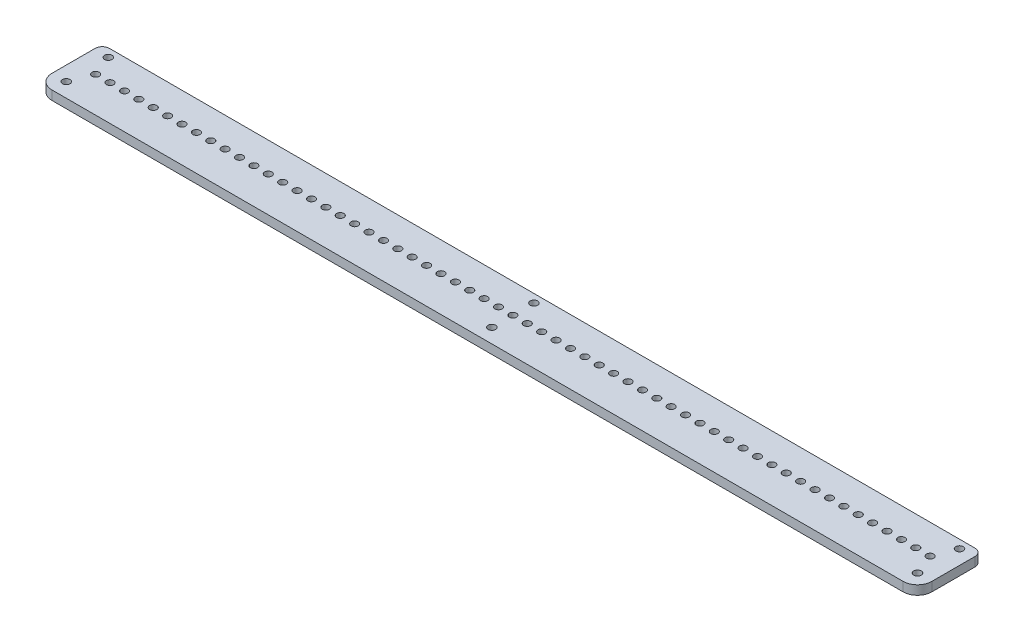
SolidWorks part; units mm, degrees
ref_plane "Front Plane" through (0, 0, 0) normal (0, 0, 1) x (1, 0, 0)
ref_plane "Top Plane" through (0, 0, 0) normal (0, 1, 0) x (1, 0, 0)
ref_plane "Right Plane" through (0, 0, 0) normal (1, 0, 0) x (0, 0, -1)
sketch "Sketch1" plane through (0, 0, 0) normal (0, 1, 0) x (1, 0, 0)
  line L1 (10, 0) -> (601.6, 0)
  line L2 (0, 10) -> (0, 40)
  line L3 (5, 45) -> (606.6, 45)
  line L4 (611.6, 10) -> (611.6, 40)
  line L5 (0, 0) -> (611.6, 45) construction
  line L6 (0, 45) -> (611.6, 0) construction
  arc A0 (0, 10) -> (10, 0) centre (10, 10) ccw
  arc A1 (611.6, 10) -> (601.6, 0) centre (601.6, 10) cw
  arc A2 (0, 40) -> (5, 45) centre (5, 40) cw
  arc A3 (611.6, 40) -> (606.6, 45) centre (606.6, 40) ccw
  point P4 (305.8, 22.5)
  dimension "D3" = 10
  dimension "D4" = 5
  dimension "D1" = 45
  dimension "D2" = 611.6
extrude "Boss-Extrude1" add sketch "Sketch1" along normal blind 6.35
sketch "Sketch5" plane through (0, 6.35, 0) normal (0, 1, 0) x (1, 0, 0)
  line L0 (10, 0) -> (601.6, 0) construction
  line L1 (611.6, 10) -> (611.6, 40) construction
  point P0 (595.8, 24.6)
  dimension "D1" = 24.6
  dimension "D2" = 15.8
hole_wizard "M6x1.0 Tapped Hole2" positions "Sketch6" profile "Sketch7" tap size "M6x1.0" standard "Autoliv NAM Metric" end condition through all
sketch "Sketch6" plane through (0, 6.35, 0) normal (0, 1, 0) x (1, 0, 0)
  point P0 (595.8, 24.6)
sketch "Sketch7" plane through (595.8, 6.35, -24.6) normal (1, 0, 0) x (0, 0, 1)
  line L0 (0, 0) -> (0, 6.35)
  line L1 (0, 6.35) -> (2.5, 6.35)
  line L2 (2.5, 6.35) -> (2.5, 0)
  line L5 (2.5, 0) -> (0, 0)
  line L11 (0, -6.35) -> (0, 107.95) construction
  dimension "Thru Tap Drill Dia." = 5
  dimension "Thru Tap Drill Depth" = 6.35
cosmetic thread "Hole Thread4" parameters "D2"=6
pattern_linear "LPattern2" count 59 spacing 10 along (-1, 0, 0) of "M6x1.0 Tapped Hole2"
sketch "Sketch8" plane through (0, 6.35, 0) normal (0, 1, 0) x (1, 0, 0)
  line L0 (305.8, 45) -> (305.8, 0) construction
  line L1 (606.6, 45) -> (5, 45) construction
  line L2 (10, 0) -> (601.6, 0) construction
  circle A0 centre (10, 10) radius 2.6
  circle A1 centre (10, 39.2) radius 2.6
  circle A2 centre (601.6, 10) radius 2.6
  circle A3 centre (601.6, 39.2) radius 2.6
  circle A4 centre (305.8, 10) radius 2.6
  arc A5 (0, 10) -> (10, 0) centre (10, 10) ccw construction
  arc A6 (601.6, 0) -> (611.6, 10) centre (601.6, 10) ccw construction
  circle A7 centre (595.8, 24.6) radius 2.5 construction
  circle A8 centre (305.8, 39.2) radius 2.6
  point P11 (305.8, 10)
  dimension "D2" = 5.2
  dimension "D1" = 14.6
extrude "Cut-Extrude1" cut sketch "Sketch8" against normal up to next
